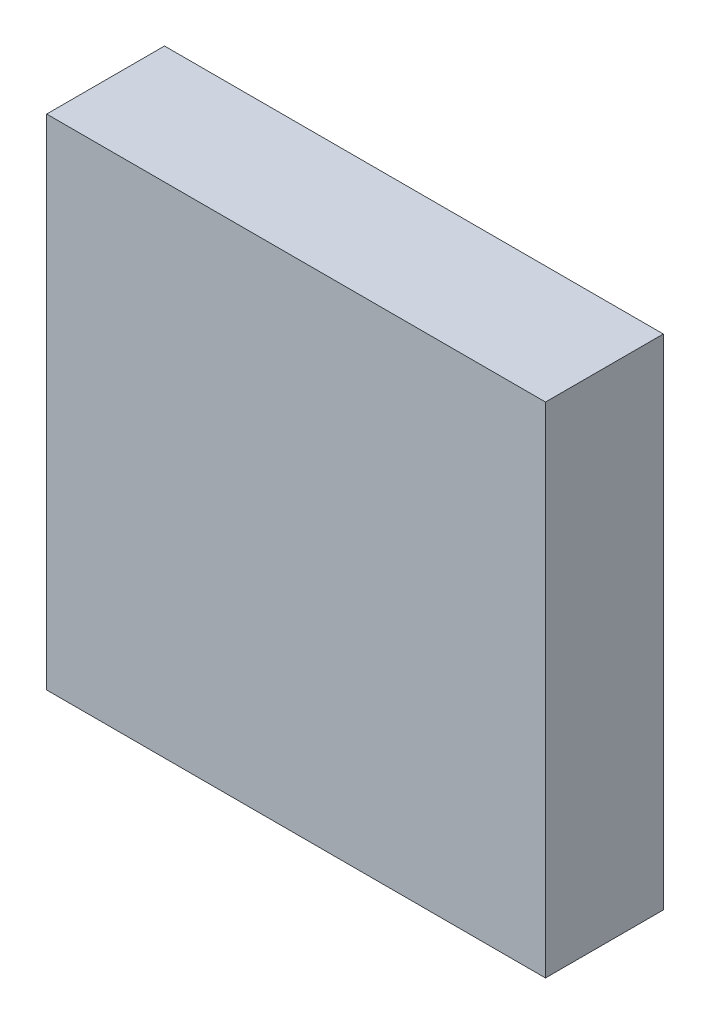
SolidWorks part; units mm, degrees
material "Glass"
ref_plane "Front Plane" through (0, 0, 0) normal (0, 0, 1) x (1, 0, 0)
ref_plane "Top Plane" through (0, 0, 0) normal (0, 1, 0) x (1, 0, 0)
ref_plane "Right Plane" through (0, 0, 0) normal (1, 0, 0) x (0, 0, -1)
sketch "Sketch1" plane through (0, 0, 0) normal (0, 0, 1) x (1, 0, 0)
  line L1 (-12.7, 12.7) -> (12.7, 12.7)
  line L2 (-12.7, 12.7) -> (-12.7, -12.7)
  line L3 (-12.7, -12.7) -> (12.7, -12.7)
  line L4 (12.7, 12.7) -> (12.7, -12.7)
  line L5 (-12.7, 12.7) -> (12.7, -12.7) construction
  line L6 (-12.7, -12.7) -> (12.7, 12.7) construction
  point P0 (0, 0)
  dimension "D1" = 25.4
extrude "Boss-Extrude1" add sketch "Sketch1" along normal blind 6
